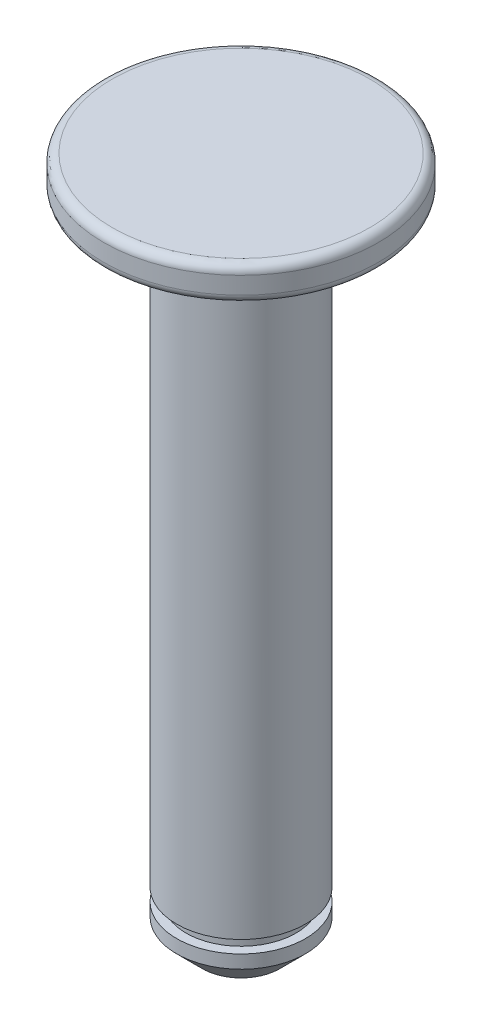
SolidWorks part; units mm, degrees
ref_plane "Front Plane" through (0, 0, 0) normal (0, 0, 1) x (1, 0, 0)
ref_plane "Top Plane" through (0, 0, 0) normal (0, 1, 0) x (1, 0, 0)
ref_plane "Right Plane" through (0, 0, 0) normal (1, 0, 0) x (0, 0, -1)
sketch "Sketch1" plane through (0, 0, 0) normal (0, 1, 0) x (1, 0, 0)
  circle A0 centre (0, 0) radius 8
  dimension "D1" = 16
extrude "Boss-Extrude1" add sketch "Sketch1" against normal blind 2
sketch "Sketch2" plane through (0, -2, 0) normal (0, -1, 0) x (1, 0, 0)
  circle A0 centre (0, 0) radius 3.75
  dimension "D1" = 7.5
extrude "Boss-Extrude2" add sketch "Sketch2" along normal blind 38
sketch "Sketch3" plane through (0, 0, 0) normal (0, 0, 1) x (1, 0, 0)
  line L0 (5.75, -2) -> (3.75, -4)
  line L1 (-8, -2) -> (8, -2) construction
  line L2 (3.75, -40) -> (3.75, -2) construction
  dimension "D1" = 45
  dimension "D2" = 2
rib "Rib2" sketch "Sketch3" sketch "Sketch3" thickness 2 extrusion direction parallel to sketch draft on no parameters "D1"=2
sketch "Sketch5" plane through (0, 0, 0) normal (1, 0, 0) x (0, 0, -1)
  line L0 (-3.75, -40) -> (3.75, -40) construction
  line L1 (5.2, -37.73) -> (3.2, -37.73)
  line L2 (5.2, -37.73) -> (5.2, -37)
  line L3 (5.2, -37) -> (3.2, -37)
  line L4 (3.2, -37.73) -> (3.2, -37)
  line L5 (5.2, -37.73) -> (3.2, -37) construction
  line L6 (5.2, -37) -> (3.2, -37.73) construction
  line L7 (0, -40) -> (0, -33.101) construction
  point P0 (4.2, -37.365)
  point P10 (3.2, -37.365)
  dimension "D1" = 0.73
  dimension "D2" = 3
  dimension "D3" = 2
  dimension "D4" = 3.2
revolve "Cut-Revolve1" cut sketch "Sketch5" angle 360 about L7
fillet "Fillet1" radius 0.5 2 edges at (0, -2, 8) (0, 0, 8)
chamfer "Chamfer1" distance 1.5 angle 45 1 edges at (0, -40, -3.75)
